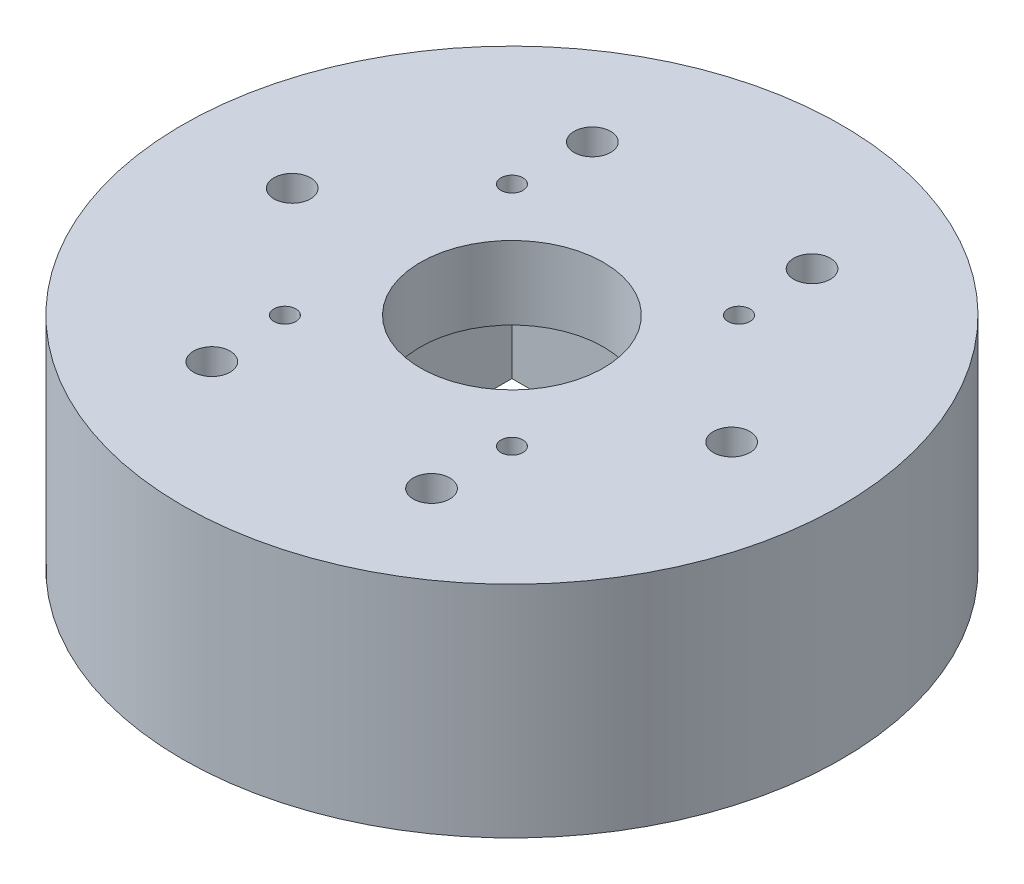
SolidWorks part; units mm, degrees
ref_plane "Front Plane" through (0, 0, 0) normal (0, 0, 1) x (1, 0, 0)
ref_plane "Top Plane" through (0, 0, 0) normal (0, 1, 0) x (1, 0, 0)
ref_plane "Right Plane" through (0, 0, 0) normal (1, 0, 0) x (0, 0, -1)
sketch "Sketch1" plane through (0, 0, 0) normal (0, 1, 0) x (1, 0, 0)
  circle A0 centre (0, 0) radius 45
  dimension "D1" = 90
extrude "Boss-Extrude1" add sketch "Sketch1" along normal blind 30
sketch "Sketch2" plane through (0, 0, 0) normal (0, -1, 0) x (1, 0, 0)
  circle A0 centre (0, 32.5) radius 4
  circle A1 centre (0, -32.5) radius 4
  dimension "D1" = 8
  dimension "D2" = 8
  dimension "D3" = 65
  dimension "D4" = 32.5
extrude "Cut-Extrude1" cut sketch "Sketch2" against normal blind 20
sketch "Sketch4" plane through (0, 0, 0) normal (0, -1, 0) x (-1, 0, 0)
  circle A0 centre (-30, 0) radius 2.5
  circle A1 centre (-15, 25.9808) radius 2.5
  circle A2 centre (15, 25.9808) radius 2.5
  circle A3 centre (30, 0) radius 2.5
  circle A4 centre (15, -25.9808) radius 2.5
  circle A5 centre (-15, -25.9808) radius 2.5
  point P15 (0, 0)
  dimension "D1" = 5
  dimension "D2" = 30
  dimension "D3" = 6
extrude "Cut-Extrude2" cut sketch "Sketch4" against normal blind 30
sketch "Sketch5" plane through (0, 0, 0) normal (0, -1, 0) x (-1, 0, 0)
  line L1 (22.5, -22.5) -> (-22.5, -22.5)
  line L2 (22.5, -22.5) -> (22.5, 22.5)
  line L3 (22.5, 22.5) -> (-22.5, 22.5)
  line L4 (-22.5, -22.5) -> (-22.5, 22.5)
  line L5 (22.5, -22.5) -> (-22.5, 22.5) construction
  line L6 (22.5, 22.5) -> (-22.5, -22.5) construction
  point P0 (0, 0)
  dimension "D1" = 45
  dimension "D2" = 45
extrude "Cut-Extrude3" cut sketch "Sketch5" against normal blind 20
sketch "Sketch6" plane through (0, 20, 0) normal (0, -1, 0) x (1, 0, 0)
  line L1 (-15.5, 15.5) -> (15.5, 15.5)
  line L2 (-15.5, 15.5) -> (-15.5, -15.5)
  line L3 (-15.5, -15.5) -> (15.5, -15.5)
  line L4 (15.5, 15.5) -> (15.5, -15.5)
  line L5 (-15.5, 15.5) -> (15.5, -15.5) construction
  line L6 (-15.5, -15.5) -> (15.5, 15.5) construction
  circle A0 centre (0, 0) radius 12.5
  circle A1 centre (-15.5, 15.5) radius 1.5
  circle A2 centre (15.5, 15.5) radius 1.5
  circle A3 centre (15.5, -15.5) radius 1.5
  circle A4 centre (-15.5, -15.5) radius 1.5
  point P0 (0, 0)
  point P15 (31, 0)
  point P18 (31, -31)
  point P21 (0, -31)
  dimension "D4" = 25
  dimension "D5" = 3
  dimension "D1" = 31
  dimension "D2" = 31
  dimension "D6" = 2
  dimension "D7" = 2
extrude "Cut-Extrude4" cut sketch "Sketch6" against normal blind 10 contours L1 A1 L2 | L2 A1 L1 | L4 A2 L1 | L1 A2 L4 | A0 | L4 A3 L3 | L3 A3 L4 | L3 A4 L2 | L2 A4 L3
